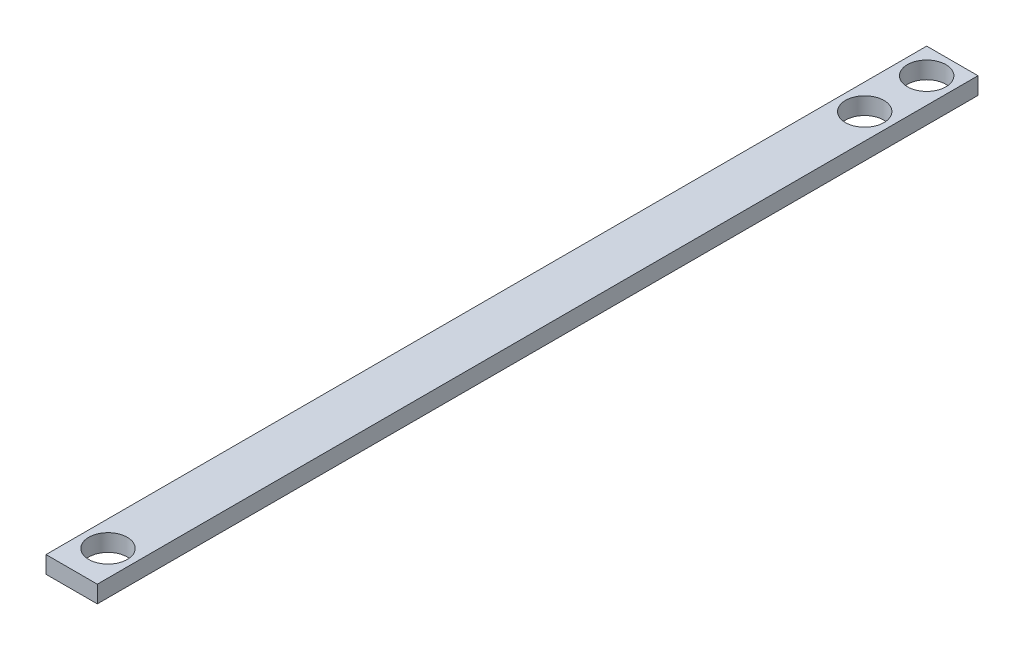
SolidWorks part; units mm, degrees
ref_plane "Front Plane" through (0, 0, 0) normal (0, 0, 1) x (1, 0, 0)
ref_plane "Top Plane" through (0, 0, 0) normal (0, 1, 0) x (1, 0, 0)
ref_plane "Right Plane" through (0, 0, 0) normal (1, 0, 0) x (0, 0, -1)
sketch "Sketch1" plane through (0, 0, 0) normal (0, 0, 1) x (1, 0, 0)
  line L1 (0, 0) -> (38.1, 0)
  line L2 (0, 0) -> (0, 12.7)
  line L3 (0, 12.7) -> (38.1, 12.7)
  line L4 (38.1, 0) -> (38.1, 12.7)
  dimension "D1" = 12.7
  dimension "D2" = 38.1
extrude "Boss-Extrude1" add sketch "Sketch1" along normal blind 615.95
sketch "Sketch2" plane through (0, 12.7, 0) normal (0, 1, 0) x (1, 0, 0)
  line L0 (38.1, -615.95) -> (0, -615.95) construction
  line L2 (38.1, 0) -> (0, 0) construction
  circle A0 centre (19.05, -588.9498) radius 14.3002
  circle A1 centre (19.05, -27.0002) radius 14.3002
  point P11 (19.05, 0)
  dimension "D1" = 28.6004
  dimension "D4" = 28.6004
  dimension "D2" = 27.0002
  dimension "D5" = 27.0002
extrude "Cut-Extrude1" cut sketch "Sketch2" against normal blind 762
sketch "Sketch3" plane through (0, 0, 0) normal (0, 0, -1) x (-1, 0, 0)
  line L1 (-38.1, 12.7) -> (0, 12.7)
  line L2 (-38.1, 12.7) -> (-38.1, 0)
  line L3 (-38.1, 0) -> (0, 0)
  line L4 (0, 12.7) -> (0, 0)
extrude "Boss-Extrude2" add sketch "Sketch3" along normal blind 38.1
sketch "Sketch4" plane through (0, 12.7, 0) normal (0, 1, 0) x (1, 0, 0)
  line L0 (0, 38.1) -> (38.1, 38.1) construction
  circle A0 centre (19.05, 19.0373) radius 14.3002
  point P5 (19.05, 38.1)
  dimension "D1" = 28.6004
  dimension "D2" = 19.0627
extrude "Cut-Extrude2" cut sketch "Sketch4" against normal blind 101.6
